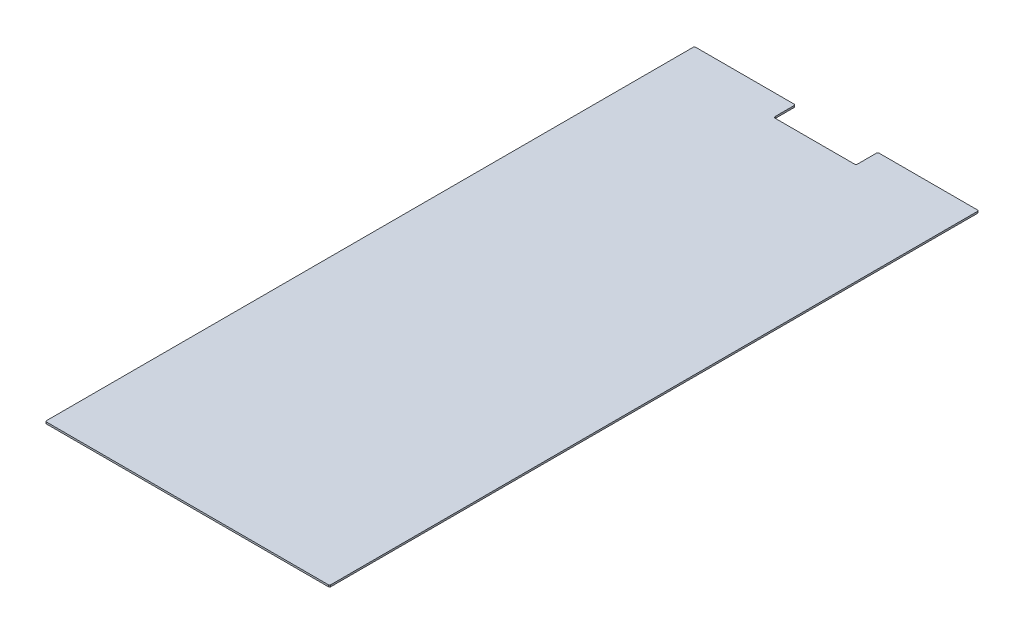
SolidWorks part; units mm, degrees
ref_plane "Front Plane" through (0, 0, 0) normal (0, 0, 1) x (1, 0, 0)
ref_plane "Top Plane" through (0, 0, 0) normal (0, 1, 0) x (1, 0, 0)
ref_plane "Right Plane" through (0, 0, 0) normal (1, 0, 0) x (0, 0, -1)
sketch "Sketch2" plane through (0, 0, 0) normal (0, 1, 0) x (1, 0, 0)
  line L0 (0, -551.5) -> (0, 551.5) construction
  line L1 (-239.5, -551.5) -> (239.5, -551.5)
  line L2 (241.5, -549.5) -> (241.5, 549.5)
  line L3 (239.5, 551.5) -> (72, 551.5)
  line L4 (70, 549.5) -> (70, 517.5)
  line L5 (67, 514.5) -> (-67, 514.5)
  line L6 (-70, 517.5) -> (-70, 549.5)
  line L7 (-72, 551.5) -> (-239.5, 551.5)
  line L8 (-241.5, 549.5) -> (-241.5, -549.5)
  arc A0 (-67, 514.5) -> (-70, 517.5) centre (-67, 517.5) cw
  arc A1 (70, 517.5) -> (67, 514.5) centre (67, 517.5) cw
  arc A2 (-239.5, 551.5) -> (-241.5, 549.5) centre (-239.5, 549.5) ccw
  arc A3 (-239.5, -551.5) -> (-241.5, -549.5) centre (-239.5, -549.5) cw
  arc A4 (239.5, -551.5) -> (241.5, -549.5) centre (239.5, -549.5) ccw
  arc A5 (241.5, 549.5) -> (239.5, 551.5) centre (239.5, 549.5) ccw
  arc A6 (72, 551.5) -> (70, 549.5) centre (72, 549.5) ccw
  arc A7 (-70, 549.5) -> (-72, 551.5) centre (-72, 549.5) ccw
  point P0 (0, 514.5)
  point P4 (0, 0)
  point P8 (0, -551.5)
  point P17 (-70, 514.5)
  point P20 (70, 514.5)
  point P25 (-241.5, -551.5)
  point P28 (241.5, -551.5)
  point P33 (70, 551.5)
  dimension "D5" = 3
  dimension "D6" = 2
  dimension "D7" = 2
  dimension "D1" = 1103
  dimension "D2" = 483
  dimension "D3" = 140
  dimension "D4" = 37
extrude "Boss-Extrude1" add sketch "Sketch2" along normal blind 3
